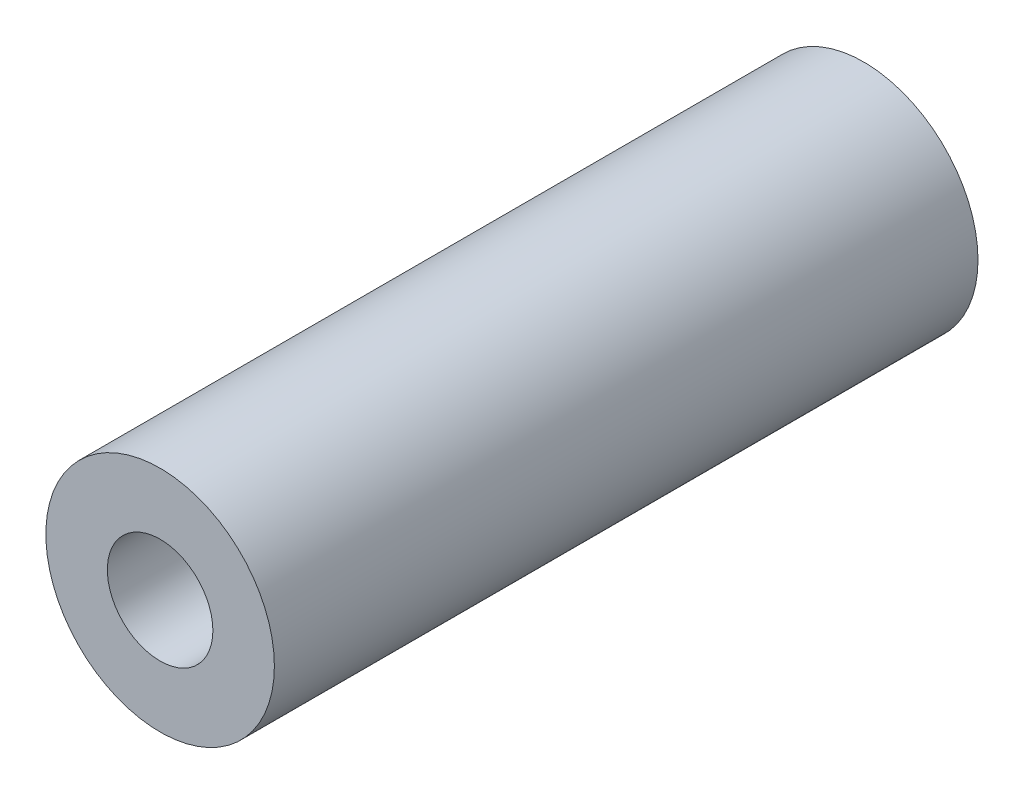
SolidWorks part; units mm, degrees
ref_plane "Front Plane" through (0, 0, 0) normal (0, 0, 1) x (1, 0, 0)
ref_plane "Top Plane" through (0, 0, 0) normal (0, 1, 0) x (1, 0, 0)
ref_plane "Right Plane" through (0, 0, 0) normal (1, 0, 0) x (0, 0, -1)
sketch "Sketch1" plane through (0, 0, 0) normal (0, 0, 1) x (1, 0, 0)
  circle A0 centre (0, 0) radius 4.7625
  circle A1 centre (0, 0) radius 10.3124
  dimension "D1" = 9.525
  dimension "D2" = 20.6248
extrude "Boss-Extrude1" add sketch "Sketch1" along normal blind 63.5
